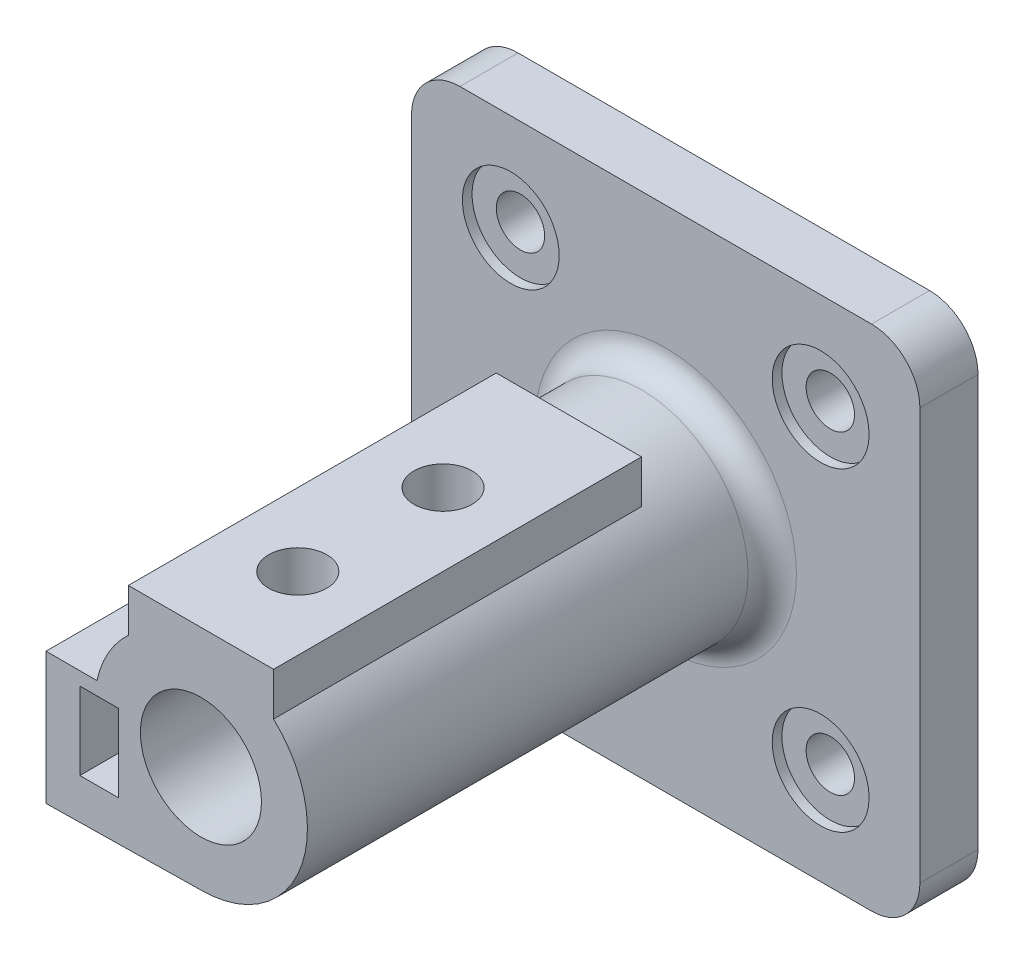
SolidWorks part; units mm, degrees
ref_plane "Front Plane" through (0, 0, 0) normal (0, 0, 1) x (1, 0, 0)
ref_plane "Top Plane" through (0, 0, 0) normal (0, 1, 0) x (1, 0, 0)
ref_plane "Right Plane" through (0, 0, 0) normal (1, 0, 0) x (0, 0, -1)
sketch "Sketch1" plane through (0, 0, 0) normal (0, 0, 1) x (1, 0, 0)
  line L1 (-52.5, 52.5) -> (52.5, 52.5)
  line L2 (-52.5, 52.5) -> (-52.5, -52.5)
  line L3 (-52.5, -52.5) -> (52.5, -52.5)
  line L4 (52.5, 52.5) -> (52.5, -52.5)
  line L5 (-52.5, 52.5) -> (52.5, -52.5) construction
  line L6 (-52.5, -52.5) -> (52.5, 52.5) construction
  point P0 (0, 0)
  dimension "D1" = 105
  dimension "D2" = 105
extrude "Boss-Extrude1" add sketch "Sketch1" along normal blind 12
sketch "Sketch2" plane through (0, 0, 12) normal (0, 0, 1) x (1, 0, 0)
  circle A0 centre (0, 0) radius 12.5
  circle A1 centre (0, 0) radius 22
  dimension "D1" = 44
  dimension "D2" = 25
extrude "Boss-Extrude2" add sketch "Sketch2" along normal blind 96
fillet "Fillet1" radius 5 1 edges at (22, 0, 12)
sketch "Sketch4" plane through (0, 0, 12) normal (0, 0, 1) x (1, 0, 0)
  line L0 (52.5, 52.5) -> (-52.5, 52.5) construction
  circle A0 centre (-32, 32.5) radius 10
  dimension "D3" = 20
  dimension "D1" = 32
  dimension "D2" = 20
extrude "Cut-Extrude2" cut sketch "Sketch4" against normal blind 2
sketch "Sketch6" plane through (0, 0, 10) normal (0, 0, 1) x (1, 0, 0)
  circle A0 centre (-32, 32.5) radius 5
  dimension "D1" = 10
extrude "Cut-Extrude3" cut sketch "Sketch6" against normal through all
mirror "Mirror2" about plane through (0, 0, 0) normal (1, 0, 0) of "Cut-Extrude3", "Cut-Extrude2"
mirror "Mirror3" about plane through (0, 0, 0) normal (0, 1, 0) of "Cut-Extrude3", "Mirror2", "Cut-Extrude2"
sketch "Sketch8" plane through (0, 0, 108) normal (0, 0, 1) x (1, 0, 0)
  line L0 (0, -22) -> (-32, -22.5)
  line L1 (-32, -22.5) -> (-32, 4.7392)
  line L2 (-32, 4.7392) -> (-21.4835, 4.7392)
  line L4 (-25, 2) -> (-17, 2)
  line L5 (-25, 2) -> (-25, -14)
  line L6 (-25, -14) -> (-17, -14)
  line L7 (-17, 2) -> (-17, -14)
  circle A0 centre (0, 0) radius 22 construction
  circle A1 centre (0, 0) radius 22 construction
  circle A2 centre (-32, -32.5) radius 10 construction
  arc A3 (-21.4835, 4.7392) -> (-21.9089, 2) centre (0, 0) ccw
  arc A4 (-17, -13.9642) -> (0, -22) centre (0, 0) ccw
  circle M3 centre (0, 0) radius 22
  dimension "D1" = 8
  dimension "D2" = 16
  dimension "D3" = 2
  dimension "D4" = 25
extrude "Boss-Extrude5" add sketch "Sketch8" against normal blind 57 contours L7 L6 L5 L4 L2 L1 L0 M3
sketch "Sketch9" plane through (0, 0, 108) normal (0, 0, 1) x (1, 0, 0)
  line L0 (-25, 2) -> (-17, 2)
  line L1 (-17, 2) -> (-17, -14)
  line L2 (-17, -14) -> (-25, -14)
  line L3 (-25, -14) -> (-25, 2)
  dimension "D1" = 8
extrude "Cut-Extrude5" cut sketch "Sketch9" against normal blind 50
sketch "Sketch10" plane through (0, 0, 108) normal (0, 0, 1) x (1, 0, 0)
  line L0 (0, 0) -> (0, 22) construction
  line L1 (-15, 25) -> (15, 25)
  line L2 (-15, 25) -> (-15, 16.0935)
  line L3 (15, 25) -> (15, 16.0935)
  circle A0 centre (0, 0) radius 22 construction
  arc A1 (15, 16.0935) -> (-15, 16.0935) centre (0, 0) ccw
  dimension "D1" = 25
extrude "Boss-Extrude6" add sketch "Sketch10" against normal blind 76
sketch "Sketch11" plane through (0, 25, 0) normal (0, 1, 0) x (1, 0, 0)
  circle A0 centre (0, -88) radius 6
  circle A1 centre (0, -58) radius 6
  dimension "D1" = 12
  dimension "D2" = 12
  dimension "D3" = 30
  dimension "D4" = 20
extrude "Cut-Extrude6" cut sketch "Sketch11" against normal up to next
fillet "Fillet2" radius 10 4 edges at (52.5, -52.5, 6) (52.5, 52.5, 6) (-52.5, -52.5, 6) (-52.5, 52.5, 6)
sketch "Sketch12" plane through (-32, 0, 0) normal (-1, 0, 0) x (0, 0, 1)
  line L0 (108, -22.5) -> (108, 4.7392) construction
  circle A0 centre (93, -8.8804) radius 5
  circle A1 centre (71, -8.8804) radius 5
  point P6 (108, -8.8804)
  dimension "D1" = 10
  dimension "D2" = 10
  dimension "D3" = 15
  dimension "D4" = 22
extrude "Cut-Extrude7" cut sketch "Sketch12" against normal up to next
